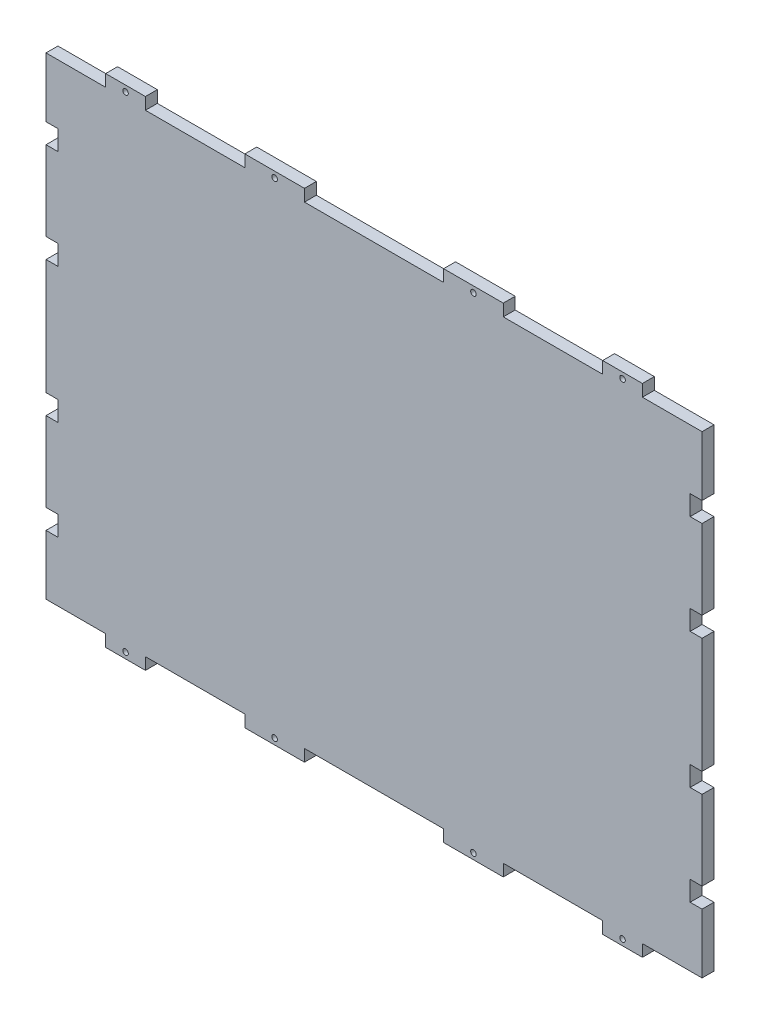
SolidWorks part; units mm, degrees
ref_plane "Plan de face" through (0, 0, 0) normal (0, 0, 1) x (1, 0, 0)
ref_plane "Plan de dessus" through (0, 0, 0) normal (0, 1, 0) x (1, 0, 0)
ref_plane "Plan de droite" through (0, 0, 0) normal (1, 0, 0) x (0, 0, -1)
sketch "Esquisse1" plane through (0, 0, 0) normal (0, 0, 1) x (1, 0, 0)
  line L0 (97.3951, 0) -> (-118.5049, 0) construction
  line L1 (-165, 119) -> (165, 119)
  line L2 (-165, 119) -> (-165, -119)
  line L3 (-165, -119) -> (165, -119)
  line L4 (165, 119) -> (165, -119)
  line L5 (0, 79.3588) -> (0, -79.3588) construction
  dimension "D1" = 238
  dimension "D2" = 330
  dimension "D3" = 165
  dimension "D4" = 119
extrude "Boss.-Extru.1" add sketch "Esquisse1" along normal blind 6
sketch "Esquisse2" plane through (0, 0, 6) normal (0, 0, 1) x (1, 0, 0)
  line L0 (243.146, 0) -> (-260.0003, 0) construction
  line L1 (0, 180.4713) -> (0, -129.6072) construction
  line L2 (165, 119) -> (-165, 119) construction
  line L3 (-135, 119) -> (-115, 119)
  line L4 (-135, 119) -> (-135, 125)
  line L5 (-135, 125) -> (-115, 125)
  line L6 (-115, 119) -> (-115, 125)
  line L7 (-165, 119) -> (-165, -119) construction
  line L8 (-65, 119) -> (-35, 119)
  line L9 (-65, 119) -> (-65, 125)
  line L10 (-65, 125) -> (-35, 125)
  line L11 (-35, 119) -> (-35, 125)
  line L12 (35, 119) -> (35, 125)
  line L13 (65, 125) -> (35, 125)
  line L14 (65, 119) -> (65, 125)
  line L15 (65, 119) -> (35, 119)
  line L16 (115, 119) -> (115, 125)
  line L17 (135, 125) -> (115, 125)
  line L18 (135, 119) -> (135, 125)
  line L19 (135, 119) -> (115, 119)
  line L20 (-135, 119) -> (-115, 119)
  line L21 (-135, 119) -> (-135, 125)
  line L22 (-135, 125) -> (-115, 125)
  line L23 (-115, 119) -> (-115, 125)
  line L24 (-65, 119) -> (-35, 119)
  line L25 (-65, 119) -> (-65, 125)
  line L26 (-65, 125) -> (-35, 125)
  line L27 (-35, 119) -> (-35, 125)
  line L28 (35, 119) -> (35, 125)
  line L29 (65, 125) -> (35, 125)
  line L30 (65, 119) -> (65, 125)
  line L31 (65, 119) -> (35, 119)
  line L32 (115, 119) -> (115, 125)
  line L33 (135, 125) -> (115, 125)
  line L34 (135, 119) -> (135, 125)
  line L35 (135, 119) -> (115, 119)
  line L36 (135, -119) -> (115, -119)
  line L37 (135, -119) -> (135, -125)
  line L38 (135, -125) -> (115, -125)
  line L39 (115, -119) -> (115, -125)
  line L40 (65, -119) -> (35, -119)
  line L41 (65, -119) -> (65, -125)
  line L42 (65, -125) -> (35, -125)
  line L43 (35, -119) -> (35, -125)
  line L44 (-35, -119) -> (-35, -125)
  line L45 (-65, -125) -> (-35, -125)
  line L46 (-65, -119) -> (-65, -125)
  line L47 (-65, -119) -> (-35, -119)
  line L48 (-115, -119) -> (-115, -125)
  line L49 (-135, -125) -> (-115, -125)
  line L50 (-135, -119) -> (-135, -125)
  line L51 (-135, -119) -> (-115, -119)
  line L52 (135, -119) -> (115, -119)
  line L53 (135, -119) -> (135, -125)
  line L54 (135, -125) -> (115, -125)
  line L55 (115, -119) -> (115, -125)
  line L56 (65, -119) -> (35, -119)
  line L57 (65, -119) -> (65, -125)
  line L58 (65, -125) -> (35, -125)
  line L59 (35, -119) -> (35, -125)
  line L60 (-35, -119) -> (-35, -125)
  line L61 (-65, -125) -> (-35, -125)
  line L62 (-65, -119) -> (-65, -125)
  line L63 (-65, -119) -> (-35, -119)
  line L64 (-115, -119) -> (-115, -125)
  line L65 (-135, -125) -> (-115, -125)
  line L66 (-135, -119) -> (-135, -125)
  line L67 (-135, -119) -> (-115, -119)
  line M9 (-165, -119) -> (165, -119)
  line M11 (165, 119) -> (-165, 119)
  dimension "D1" = 6
  dimension "D2" = 6
  dimension "D3" = 20
  dimension "D4" = 30
  dimension "D5" = 30
  dimension "D6" = 50
extrude "Boss.-Extru.2" add sketch "Esquisse2" against normal blind 6 contours L6 L5 L4 M11 | L11 L10 L9 M11 | L14 L13 L12 M11 | L18 L17 L16 M11 | L39 L38 L37 M9 | L43 L42 L41 M9 | L46 L45 L44 M9 | L50 L49 L48 M9
sketch "Esquisse3" plane through (0, 0, 6) normal (0, 0, 1) x (1, 0, 0)
  line L0 (-165, 119) -> (-165, -119) construction
  line L1 (-165, 79) -> (-159, 79)
  line L2 (-165, 79) -> (-165, 89)
  line L3 (-165, 89) -> (-159, 89)
  line L4 (-159, 79) -> (-159, 89)
  line L5 (234.1368, 0) -> (-337.9213, 0) construction
  line L6 (-165, 39) -> (-159, 39)
  line L7 (-165, 39) -> (-165, 29)
  line L8 (-165, 29) -> (-159, 29)
  line L9 (-159, 39) -> (-159, 29)
  line L10 (0, 279.7488) -> (0, -188.1201) construction
  line L11 (-135, 119) -> (-165, 119) construction
  line L12 (-159, -39) -> (-159, -29)
  line L13 (-165, -29) -> (-159, -29)
  line L14 (-165, -39) -> (-165, -29)
  line L15 (-165, -39) -> (-159, -39)
  line L16 (-159, -79) -> (-159, -89)
  line L17 (-165, -89) -> (-159, -89)
  line L18 (-165, -79) -> (-165, -89)
  line L19 (-165, -79) -> (-159, -79)
  line L20 (165, -79) -> (159, -79)
  line L21 (165, -79) -> (165, -89)
  line L22 (165, -89) -> (159, -89)
  line L23 (159, -79) -> (159, -89)
  line L24 (165, -39) -> (159, -39)
  line L25 (165, -39) -> (165, -29)
  line L26 (165, -29) -> (159, -29)
  line L27 (159, -39) -> (159, -29)
  line L28 (159, 39) -> (159, 29)
  line L29 (165, 29) -> (159, 29)
  line L30 (165, 39) -> (165, 29)
  line L31 (165, 39) -> (159, 39)
  line L32 (159, 79) -> (159, 89)
  line L33 (165, 89) -> (159, 89)
  line L34 (165, 79) -> (165, 89)
  line L35 (165, 79) -> (159, 79)
  dimension "D1" = 40
  dimension "D2" = 6
  dimension "D3" = 6
  dimension "D4" = 10
  dimension "D5" = 10
  dimension "D6" = 30
extrude "Enlèv. mat.-Extru.1" cut sketch "Esquisse3" against normal blind 6
sketch "Esquisse4" plane through (0, 0, 6) normal (0, 0, 1) x (1, 0, 0)
  line L0 (-135, 119) -> (-135, 125) construction
  line L2 (0, 187.2979) -> (0, -168.1338) construction
  line L3 (-252.9265, 0) -> (316.4029, 0) construction
  line L4 (-65, 125) -> (-35, 125) construction
  line L5 (-65, 119) -> (-65, 125) construction
  circle A0 centre (-125, 122) radius 1.4
  circle A1 centre (-50, 122) radius 1.4
  circle A2 centre (50, 122) radius 1.4
  circle A3 centre (125, 122) radius 1.4
  circle A4 centre (125, -122) radius 1.4
  circle A5 centre (50, -122) radius 1.4
  circle A6 centre (-50, -122) radius 1.4
  circle A7 centre (-125, -122) radius 1.4
  dimension "D1" = 2.8
  dimension "D2" = 10
  dimension "D4" = 2.8
  dimension "D5" = 3
  dimension "D6" = 15
extrude "Enlèv. mat.-Extru.2" cut sketch "Esquisse4" against normal blind 6
equation "\"D3@Esquisse1\"=\"D2@Esquisse1\"/2"
equation "\"D4@Esquisse1\"=\"D1@Esquisse1\"/2"
